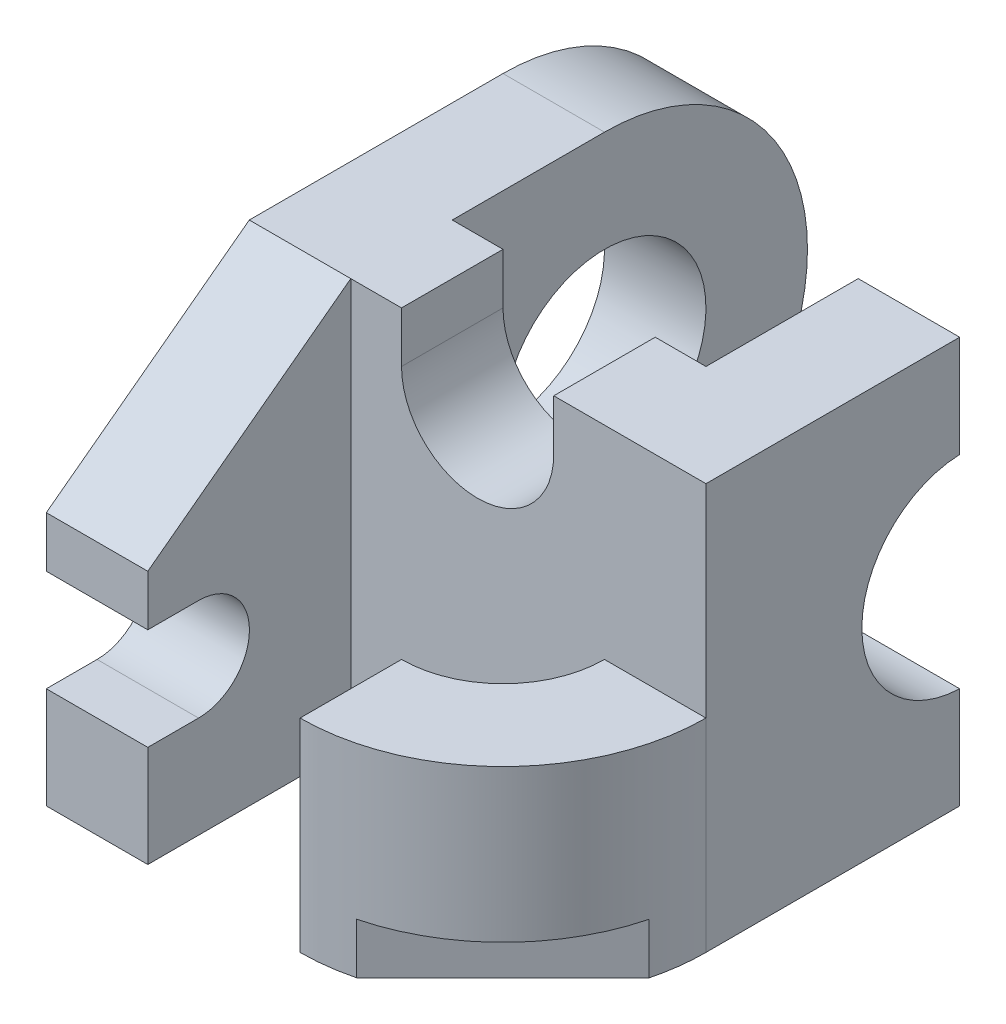
SolidWorks part; units mm, degrees
ref_plane "Front Plane" through (0, 0, 0) normal (0, 0, 1) x (1, 0, 0)
ref_plane "Top Plane" through (0, 0, 0) normal (0, 1, 0) x (1, 0, 0)
ref_plane "Right Plane" through (0, 0, 0) normal (1, 0, 0) x (0, 0, -1)
sketch "Sketch1" plane through (0, 0, 0) normal (0, 0, 1) x (1, 0, 0)
  line L0 (-3, 0) -> (-6, 0)
  line L1 (-6, 0) -> (-6, -8)
  line L2 (-6, -8) -> (3, -8)
  line L3 (3, -8) -> (3, 0)
  line L4 (3, 0) -> (0, 0)
  line L5 (-3, 0) -> (-3, -1)
  line L6 (0, 0) -> (0, -1)
  arc A0 (-3, -1) -> (0, -1) centre (-1.5, -1) ccw
  dimension "D1" = 3
  dimension "D2" = 3
  dimension "D3" = 1
  dimension "D4" = 1
  dimension "D5" = 3
  dimension "D6" = 8
extrude "Boss-Extrude1" add sketch "Sketch1" along normal blind 2
sketch "Sketch2" plane through (3, 0, 0) normal (1, 0, 0) x (0, 0, -1)
  line L0 (0, 0) -> (3, 0)
  line L1 (3, 0) -> (3, -2.0026)
  line L2 (0, 0) -> (0, -8)
  line L3 (0, -8) -> (3, -8)
  line L4 (3, -8) -> (3, -6)
  arc A0 (3, -2.0026) -> (3, -6) centre (3.0717, -4.0013) ccw
  dimension "D1" = 3
  dimension "D2" = 2.0026
  dimension "D3" = 2
  dimension "D4" = 2
extrude "Boss-Extrude2" add sketch "Sketch2" against normal blind 2
sketch "Sketch3" plane through (-6, 0, 0) normal (-1, 0, 0) x (0, 0, 1)
  line L0 (-3, 0) -> (0, 0)
  line L1 (0, 0) -> (0, -8)
  line L2 (0, -8) -> (-3, -8)
  arc A0 (-3, 0) -> (-3, -8) centre (-3, -4) ccw
  circle A1 centre (-3, -4) radius 2
  dimension "D1" = 4
extrude "Boss-Extrude3" add sketch "Sketch3" against normal blind 2
sketch "Sketch4" plane through (-6, 0, 0) normal (-1, 0, 0) x (0, 0, 1)
  line L0 (6, -8) -> (2, -8)
  line L1 (2, -8) -> (2, 0)
  line L2 (2, 0) -> (6, -2.9944)
  line L3 (6, -2.9944) -> (6, -3.9944)
  line L4 (6, -3.9944) -> (5, -3.9944)
  line L5 (6, -8) -> (6, -6)
  line L6 (6, -6) -> (5, -6)
  arc A0 (5, -3.9944) -> (5, -6) centre (5, -4.9972) ccw
  dimension "D6" = 1.0028
  dimension "D1" = 4
  dimension "D2" = 2
  dimension "D3" = 1
  dimension "D4" = 1
  dimension "D5" = 1
extrude "Boss-Extrude4" add sketch "Sketch4" against normal blind 2
sketch "Sketch5" plane through (0, -8, 0) normal (0, -1, 0) x (1, 0, 0)
  line L0 (3, 2) -> (1, 2)
  line L1 (-4, 2) -> (3, 2) construction
  line L2 (-1, 6) -> (-1, 4)
  line L3 (0, 2) -> (-3, 2) construction
  arc A0 (1, 2) -> (-1, 4) centre (-1, 2) ccw
  arc A1 (-1, 6) -> (3, 2) centre (-1, 2) cw
  point P7 (-1.5, 2)
  dimension "D5" = 2
  dimension "D6" = 4
  dimension "D1" = 2
  dimension "D2" = 2
  dimension "D3" = 2
  dimension "D4" = 4
extrude "Boss-Extrude5" add sketch "Sketch5" against normal blind 4
sketch "Sketch6" plane through (0, -8, 0) normal (0, -1, 0) x (1, 0, 0)
  line L0 (-0.0078, 5.875) -> (2.873, 3)
  arc A0 (3, 2) -> (-1, 6) centre (-1, 2) ccw construction
  arc A1 (-0.0078, 5.875) -> (2.873, 3) centre (-1, 2) cw
  dimension "D1" = 1
  dimension "D2" = 1
extrude "Cut-Extrude1" cut sketch "Sketch6" against normal blind 1
